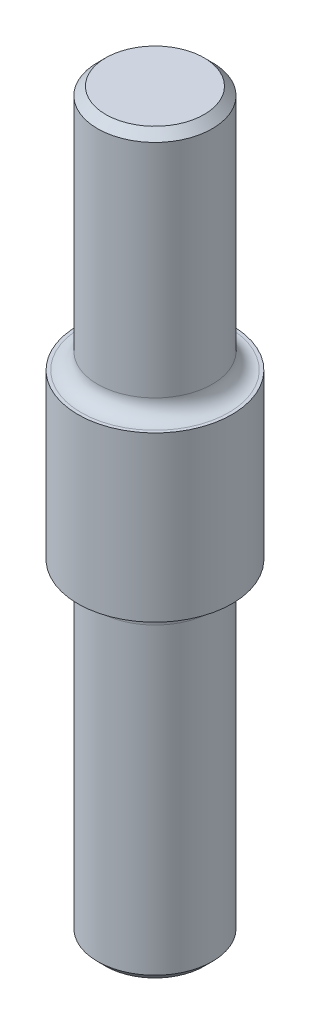
SolidWorks part; units mm, degrees
ref_plane "Front Plane" through (0, 0, 0) normal (0, 0, 1) x (1, 0, 0)
ref_plane "Top Plane" through (0, 0, 0) normal (0, 1, 0) x (1, 0, 0)
ref_plane "Right Plane" through (0, 0, 0) normal (1, 0, 0) x (0, 0, -1)
sketch "Sketch1" plane through (0, 0, 0) normal (0, 1, 0) x (1, 0, 0)
  circle A0 centre (0, 0) radius 3.5
  dimension "D1" = 7
extrude "Boss-Extrude1" add sketch "Sketch1" along normal blind 20
cosmetic thread "Cosmetic Thread1" parameters "D1"=17.5, "D2"=5.891
sketch "Sketch2" plane through (0, 20, 0) normal (0, 1, 0) x (1, 0, 0)
  circle A0 centre (0, 0) radius 4.7
  dimension "D1" = 9.4
extrude "Boss-Extrude2" add sketch "Sketch2" along normal blind 10
sketch "Sketch3" plane through (0, 30, 0) normal (0, 1, 0) x (1, 0, 0)
  circle A0 centre (0, 0) radius 3.5
  dimension "D1" = 7
extrude "Boss-Extrude3" add sketch "Sketch3" along normal blind 15
cosmetic thread "Cosmetic Thread2" parameters "D1"=15, "D2"=5.891
fillet "Fillet1" radius 1 2 edges at (0, 30, 3.5) (0, 20, 3.5)
chamfer "Chamfer1" distance 0.5 angle 45 2 edges at (0, 45, 3.5) (0, 0, 3.5)
